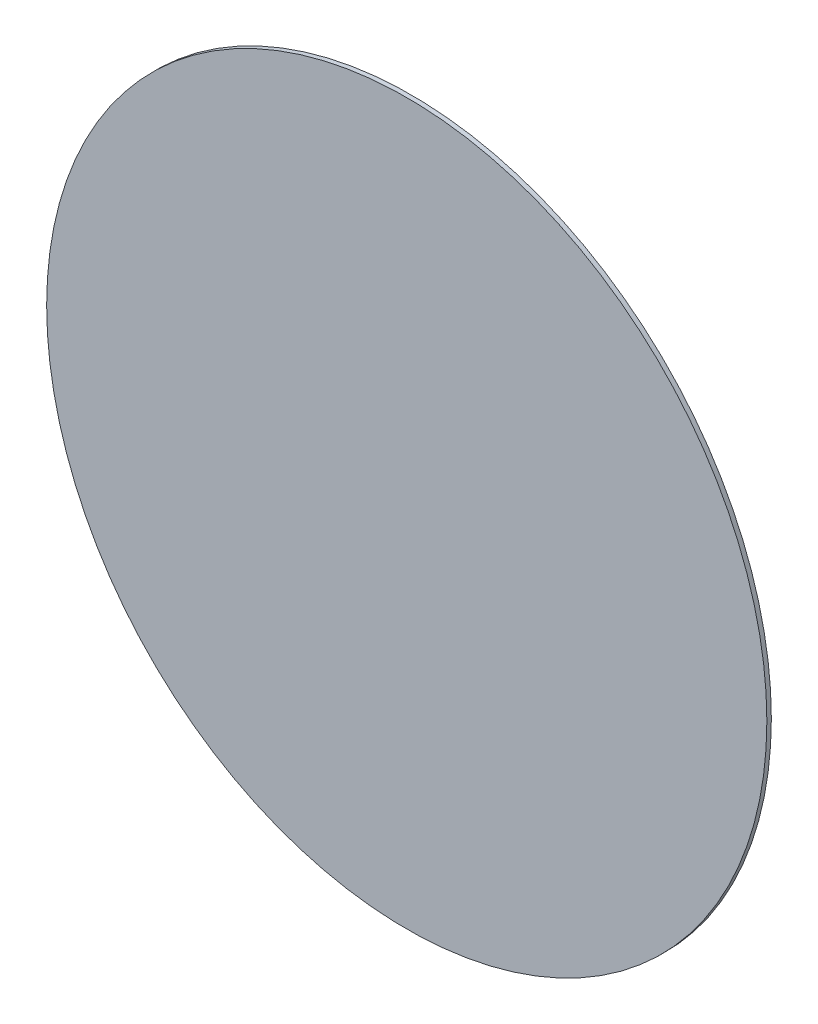
SolidWorks part; units mm, degrees
ref_plane "Plano frontal" through (0, 0, 0) normal (0, 0, 1) x (1, 0, 0)
ref_plane "Plano superior" through (0, 0, 0) normal (0, 1, 0) x (1, 0, 0)
ref_plane "Plano direito" through (0, 0, 0) normal (1, 0, 0) x (0, 0, -1)
sketch "Esboço1" plane through (0, 0, 38931.7002) normal (0, 0, 1) x (1, 0, 0)
  circle A0 centre (-33142.7874, -18960.9498) radius 801.3833
extrude "Ressalto-extrusão1" add sketch "Esboço1" along normal blind 10
